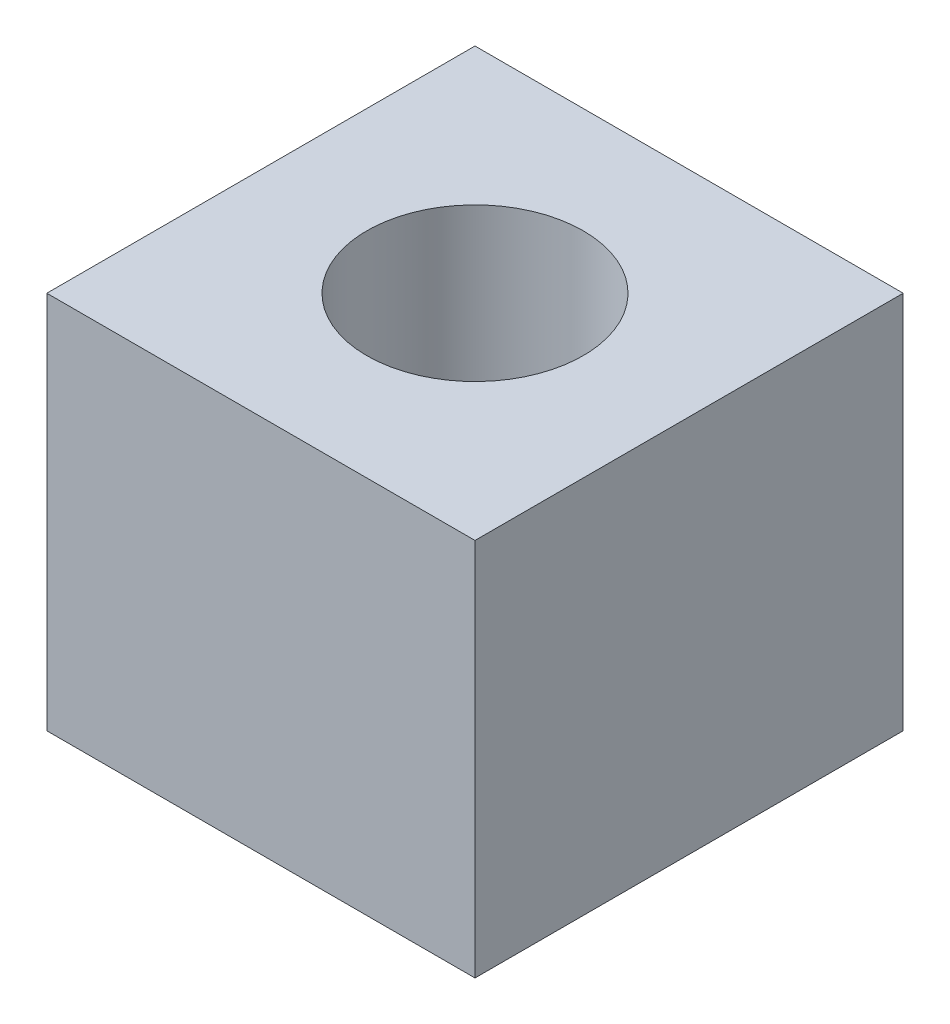
SolidWorks part; units mm, degrees
ref_plane "Front Plane" through (0, 0, 0) normal (0, 0, 1) x (1, 0, 0)
ref_plane "Top Plane" through (0, 0, 0) normal (0, 1, 0) x (1, 0, 0)
ref_plane "Right Plane" through (0, 0, 0) normal (1, 0, 0) x (0, 0, -1)
sketch "Sketch1" plane through (0, 0, 0) normal (0, 1, 0) x (1, 0, 0)
  line L1 (0, 0) -> (10, 0)
  line L2 (0, 0) -> (0, 10)
  line L3 (0, 10) -> (10, 10)
  line L4 (10, 0) -> (10, 10)
  dimension "D3" = 10
  dimension "D4" = 10
extrude "Boss-Extrude1" add sketch "Sketch1" along normal blind 8.85
sketch "Sketch2" plane through (0, 8.85, 0) normal (0, 1, 0) x (1, 0, 0)
  line L0 (0, 10) -> (0, 0) construction
  line L1 (0, 0) -> (10, 0) construction
  circle A0 centre (5, 5) radius 2.5273
  point P6 (4.8745, 4.9512)
  dimension "D1" = 5.0546
  dimension "D2" = 5
  dimension "D3" = 5
extrude "Cut-Extrude1" cut sketch "Sketch2" against normal blind 4
